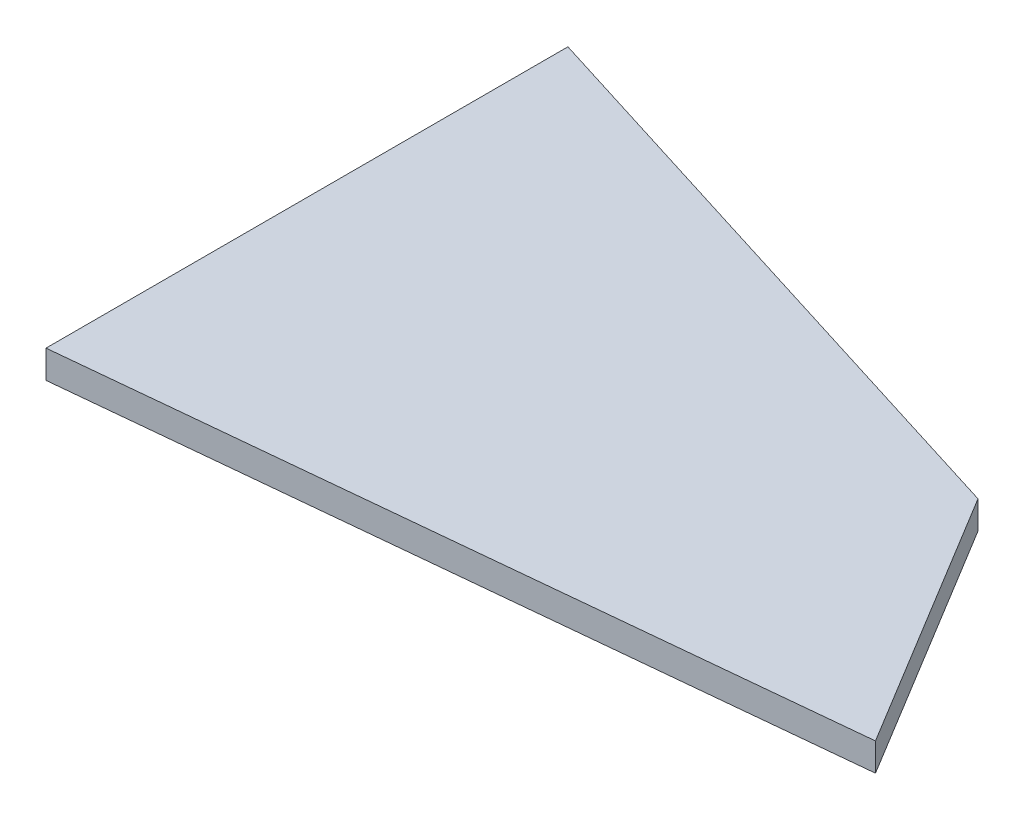
SolidWorks part; units mm, degrees
material "Plain Carbon Steel"
ref_plane "Front Plane" through (0, 0, 0) normal (0, 0, 1) x (1, 0, 0)
ref_plane "Top Plane" through (0, 0, 0) normal (0, 1, 0) x (1, 0, 0)
ref_plane "Right Plane" through (0, 0, 0) normal (1, 0, 0) x (0, 0, -1)
sketch "Sketch1" plane through (0, 0, 0) normal (0, 1, 0) x (1, 0, 0)
  line L0 (0, 0) -> (0, 88.9)
  line L1 (0, 88.9) -> (101.6, 57.15)
  line L2 (128.5875, 12.7) -> (0, 0)
  line L3 (101.6, 57.15) -> (128.5875, 12.7)
  dimension "D1" = 88.9
  dimension "D2" = 128.5875
  dimension "D3" = 12.7
  dimension "D4" = 101.6
  dimension "D5" = 57.15
extrude "Boss-Extrude1" add sketch "Sketch1" along normal blind 4.7625
